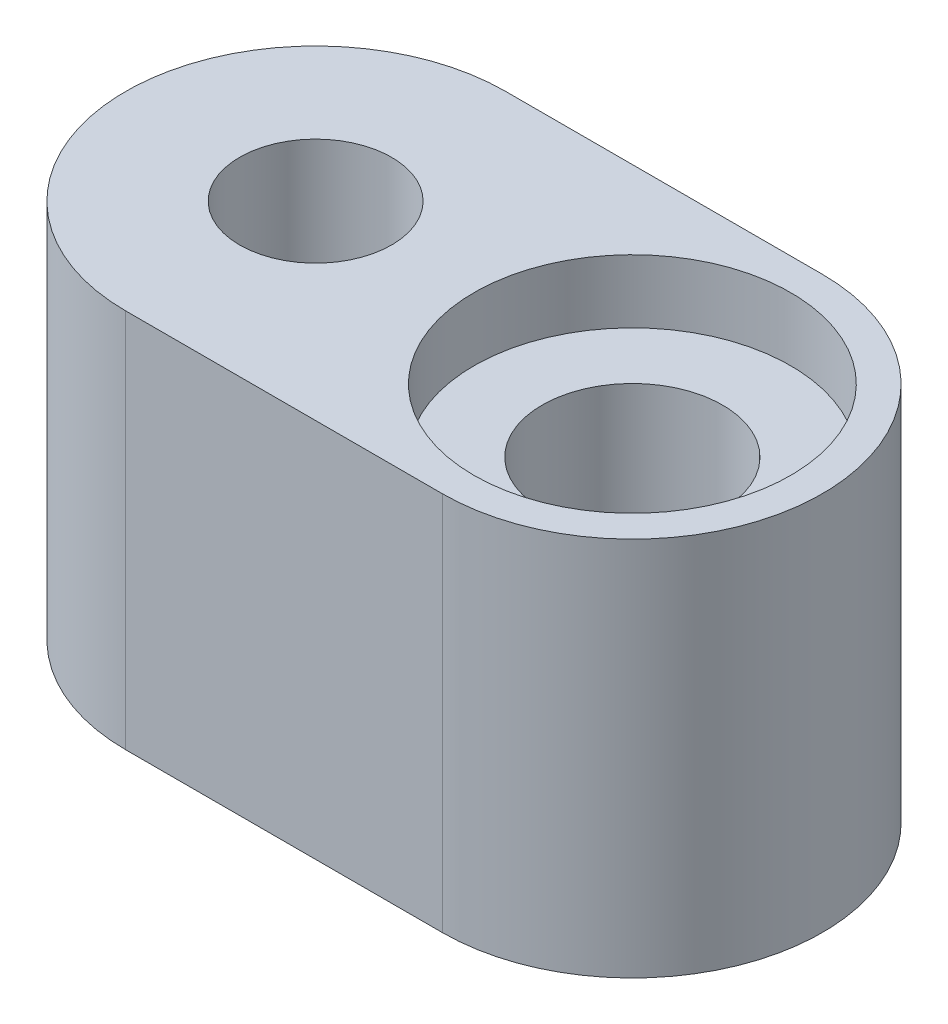
SolidWorks part; units mm, degrees
ref_plane "前视基准面" through (0, 0, 0) normal (0, 0, 1) x (1, 0, 0)
ref_plane "上视基准面" through (0, 0, 0) normal (0, 1, 0) x (1, 0, 0)
ref_plane "右视基准面" through (0, 0, 0) normal (1, 0, 0) x (0, 0, -1)
other "Configuration Table"
sketch "草图1" plane through (0, 0, 0) normal (0, 1, 0) x (1, 0, 0)
  line L0 (-2.5, 0) -> (2.5, 0) construction
  line L1 (-2.5, 3) -> (2.5, 3)
  line L2 (-2.5, -3) -> (2.5, -3)
  arc A1 (-2.5, 3) -> (-2.5, -3) centre (-2.5, 0) ccw
  arc A2 (2.5, -3) -> (2.5, 3) centre (2.5, 0) ccw
  circle A3 centre (2.5, 0) radius 1.425
  circle A4 centre (-2.5, 0) radius 1.2
  point P3 (0, 0)
  dimension "D1" = 2.4
  dimension "D2" = 2.85
  dimension "D3" = 3
  dimension "D4" = 5
extrude "凸台-拉伸1" add sketch "草图1" along normal blind 6
sketch "草图2" plane through (0, 6, 0) normal (0, 1, 0) x (1, 0, 0)
  circle A0 centre (2.5, 0) radius 2.5
  dimension "D1" = 5
extrude "切除-拉伸1" cut sketch "草图2" against normal blind 1
